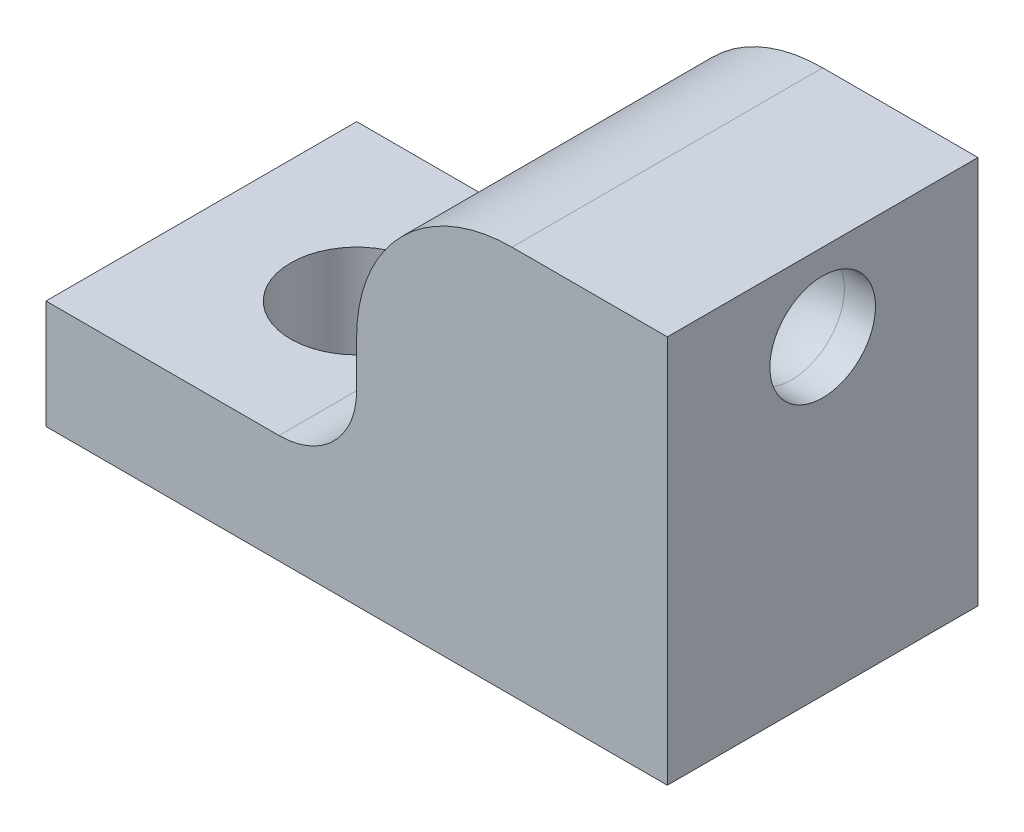
SolidWorks part; units mm, degrees
ref_plane "前基準面" through (0, 0, 0) normal (0, 0, 1) x (1, 0, 0)
ref_plane "上基準面" through (0, 0, 0) normal (0, 1, 0) x (1, 0, 0)
ref_plane "右基準面" through (0, 0, 0) normal (1, 0, 0) x (0, 0, -1)
sketch "草圖1" plane through (0, 0, 0) normal (0, 0, 1) x (1, 0, 0)
  line L1 (20, 25) -> (0, 25)
  line L2 (20, 25) -> (20, 0)
  line L7 (20, 0) -> (0, 0)
  line L8 (0, 25) -> (0, 0)
  line L9 (-20, 7) -> (0, 7)
  line L10 (-20, 7) -> (-20, 0)
  line L11 (-20, 0) -> (0, 0)
  line L12 (0, 7) -> (0, 0)
  line L13 (-20, 7) -> (0, 0) construction
  line L14 (-20, 0) -> (0, 7) construction
  line L15 (20, 25) -> (0, 0) construction
  line L16 (20, 0) -> (0, 25) construction
  point P0 (-10, 3.5)
  point P4 (10, 12.5)
  dimension "D1" = 20
  dimension "D2" = 25
  dimension "D3" = 7
  dimension "D4" = 20
extrude "填料-伸長1" add sketch "草圖1" along normal mid plane 20
sketch "草圖2" plane through (0, 7, 0) normal (0, 1, 0) x (1, 0, 0)
  line L0 (-13.75, 0) -> (13.75, 0) construction
  line L1 (-20, -10) -> (-20, 10) construction
  circle A0 centre (-10, 0) radius 4.25
  dimension "D2" = 8.5
  dimension "D1" = 10
extrude "除料-伸長1" cut sketch "草圖2" against normal through all
ref_plane "平面1" through (10, 0, 0) normal (1, 0, 0) x (0, 0, -1)
sketch "草圖4" plane through (0, 0, 0) normal (0, -1, 0) x (1, 0, 0)
  line L0 (13.75, 0) -> (-13.75, 0) construction
  line L2 (20, 10) -> (20, -10) construction
  circle A0 centre (10, 0) radius 3.4
  dimension "D1" = 6.8
  dimension "D2" = 10
sketch "草圖5" plane through (20, 0, 0) normal (0, 0, -1) x (-1, 0, 0)
  line L0 (10, 0) -> (10, 12)
  line L1 (6.6, 0) -> (13.4, 0) construction
  line L2 (2, 20) -> (0, 20)
  line L3 (0, 25) -> (0, 0) construction
  line L4 (31, 0) -> (9, 0) construction
  arc A0 (10, 12) -> (2, 20) centre (2, 12) ccw
  point P4 (5.9232, 20)
  dimension "D2" = 8
  dimension "D1" = 20
sweep "除料-掃出1" cut profiles "草圖4" path "草圖5"
fillet "圓角1" radius 5 1 edges at (0, 7, 0)
fillet "圓角2" radius 10 1 edges at (0, 25, 0)
